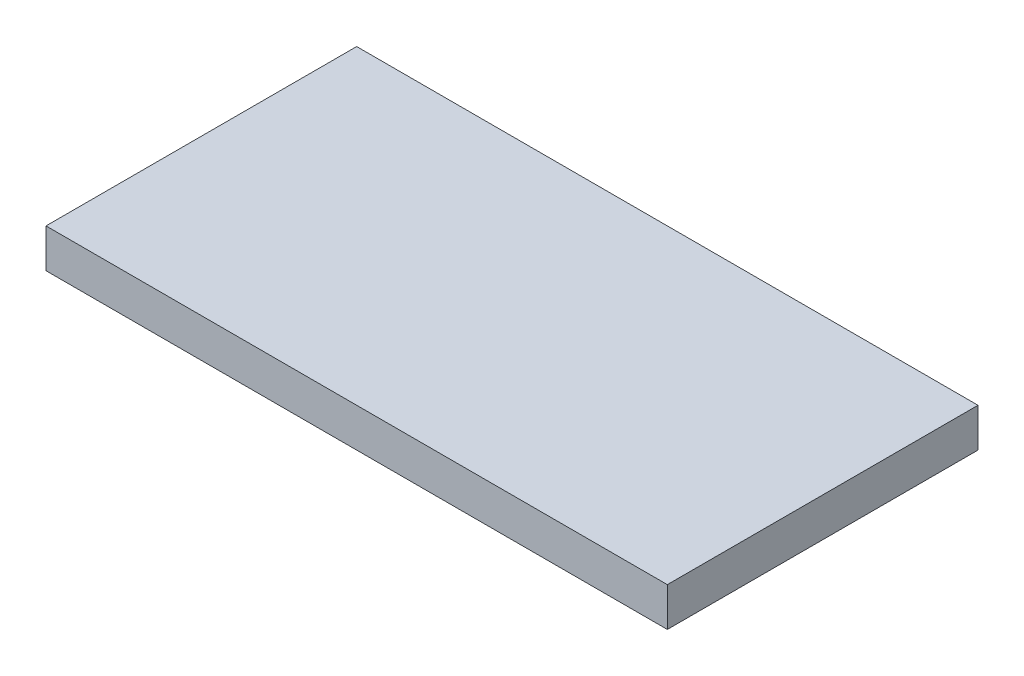
SolidWorks part; units mm, degrees
ref_plane "Front Plane" through (0, 0, 0) normal (0, 0, 1) x (1, 0, 0)
ref_plane "Top Plane" through (0, 0, 0) normal (0, 1, 0) x (1, 0, 0)
ref_plane "Right Plane" through (0, 0, 0) normal (1, 0, 0) x (0, 0, -1)
sketch "Sketch1" plane through (0, 0, 0) normal (0, 1, 0) x (1, 0, 0)
  line L1 (0, 0) -> (76.2, 0)
  line L2 (0, 0) -> (0, -38.1)
  line L3 (0, -38.1) -> (76.2, -38.1)
  line L4 (76.2, 0) -> (76.2, -38.1)
  dimension "D1" = 38.1
  dimension "D2" = 76.2
extrude "Boss-Extrude1" add sketch "Sketch1" along normal blind 4.7625 contours L1 L4 L3 L2
